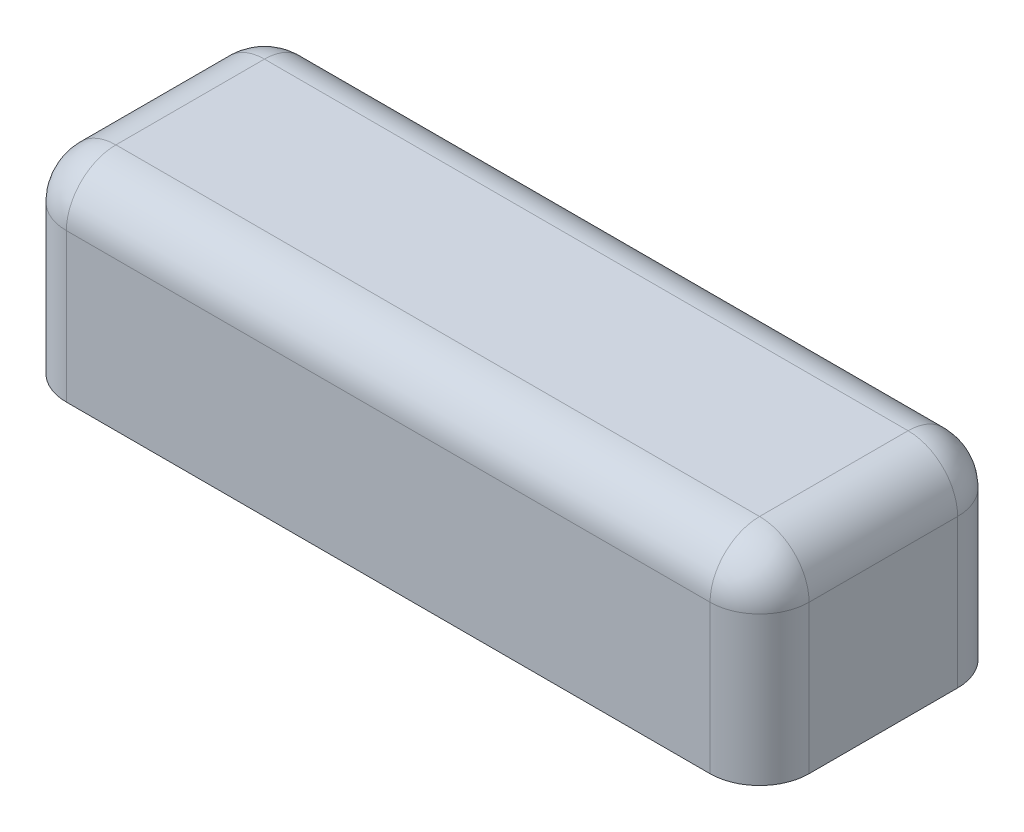
SolidWorks part; units mm, degrees
ref_plane "Front Plane" through (0, 0, 0) normal (0, 0, 1) x (1, 0, 0)
ref_plane "Top Plane" through (0, 0, 0) normal (0, 1, 0) x (1, 0, 0)
ref_plane "Right Plane" through (0, 0, 0) normal (1, 0, 0) x (0, 0, -1)
sketch "Sketch2" plane through (0, 0, 0) normal (0, 1, 0) x (1, 0, 0)
  line L0 (19.4027, -45.8353) -> (34.4027, -45.8353)
  line L1 (34.4027, -45.8353) -> (34.4027, -50.8353)
  line L2 (34.4027, -50.8353) -> (19.4027, -50.8353)
  line L3 (19.4027, -50.8353) -> (19.4027, -45.8353)
  dimension "D1" = 5
  dimension "D2" = 15
extrude "Boss-Extrude1" add sketch "Sketch2" along normal blind 4
fillet "Fillet1" radius 1 8 edges at (34.4027, 4, 48.3353) (34.4027, 2, 45.8353) (34.4027, 2, 50.8353) (19.4027, 2, 45.8353) (19.4027, 2, 50.8353) (19.4027, 4, 48.3353) (26.9027, 4, 50.8353) (26.9027, 4, 45.8353)
